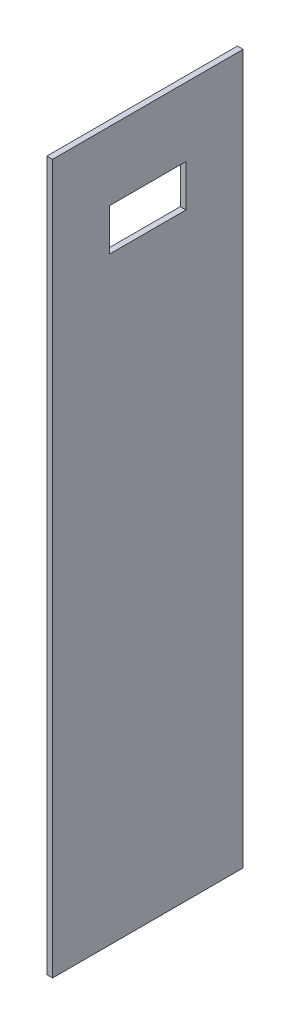
SolidWorks part; units mm, degrees
ref_plane "Front Plane" through (0, 0, 0) normal (0, 0, 1) x (1, 0, 0)
ref_plane "Top Plane" through (0, 0, 0) normal (0, 1, 0) x (1, 0, 0)
ref_plane "Right Plane" through (0, 0, 0) normal (1, 0, 0) x (0, 0, -1)
sketch "Sketch1" plane through (0, 0, 0) normal (0, 1, 0) x (1, 0, 0)
  line L1 (-0.75, 25) -> (0.75, 25)
  line L2 (-0.75, 25) -> (-0.75, -25)
  line L3 (-0.75, -25) -> (0.75, -25)
  line L4 (0.75, 25) -> (0.75, -25)
  line L5 (-0.75, 25) -> (0.75, -25) construction
  line L6 (-0.75, -25) -> (0.75, 25) construction
  point P0 (0, 0)
  dimension "D1" = 50
  dimension "D2" = 1.5
extrude "Boss-Extrude1" add sketch "Sketch1" along normal mid plane 186
sketch "Sketch3" plane through (-0.75, 0, 0) normal (-1, 0, 0) x (0, 0, 1)
  line L0 (-25, 93) -> (25, 93) construction
  line L1 (10, 75) -> (-10, 75)
  line L2 (10, 75) -> (10, 64)
  line L3 (10, 64) -> (-10, 64)
  line L4 (-10, 75) -> (-10, 64)
  line L5 (0, 75) -> (0, 93) construction
  dimension "D1" = 18
  dimension "D2" = 11
  dimension "D3" = 20
extrude "Switch" cut sketch "Sketch3" against normal through all
